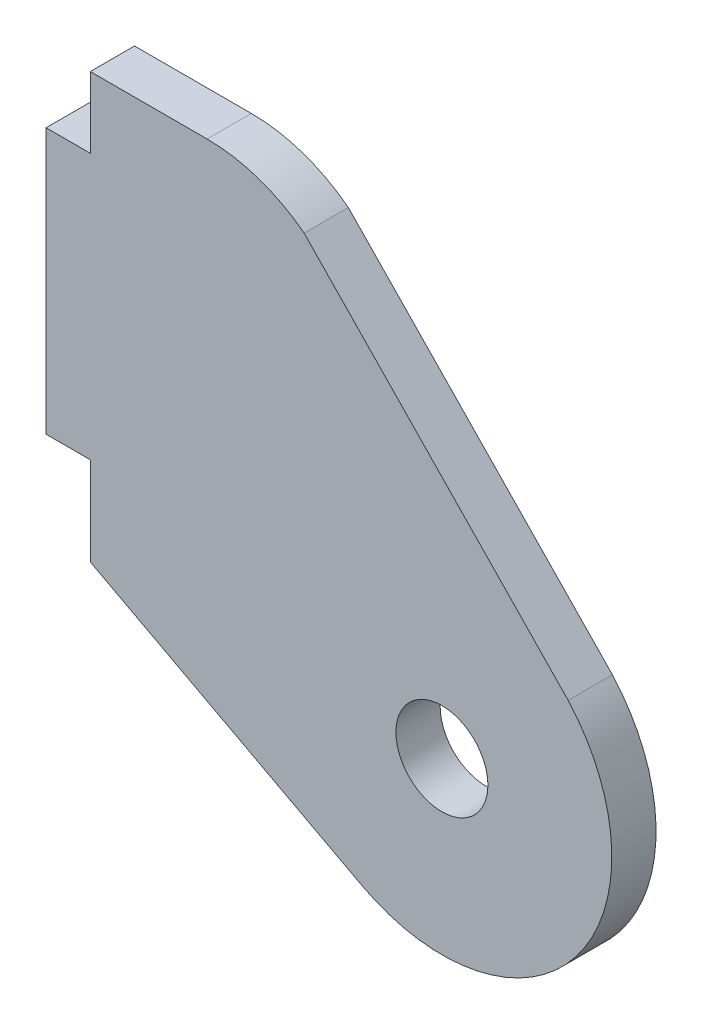
SolidWorks part; units mm, degrees
material "AISI 4130 Steel, annealed at 865C"
ref_plane "X-Y Datum" through (0, 0, 0) normal (0, 0, 1) x (1, 0, 0)
ref_plane "X-Z Datum" through (0, 0, 0) normal (0, 1, 0) x (1, 0, 0)
ref_plane "Y-Z Datum" through (0, 0, 0) normal (1, 0, 0) x (0, 0, -1)
sketch "Sketch1" plane through (0, 0, 0) normal (0, 0, 1) x (1, 0, 0)
  line L8 (-79.4095, -48.8706) -> (-79.4095, -29.8206)
  line L9 (-79.4095, -29.8206) -> (-76.2345, -29.8206)
  line L10 (-76.2345, -29.8206) -> (-76.2345, -24.7406)
  line L11 (-76.2345, -24.7406) -> (-67.8525, -24.7406)
  line L12 (-79.4095, -48.8706) -> (-76.2345, -48.8706)
  line L13 (-76.2345, -48.8706) -> (-76.2345, -55.2206)
  line L14 (-76.2345, -55.2206) -> (-56.7232, -65.595)
  line L18 (-60.8897, -27.1062) -> (-41.9389, -46.672)
  arc A2 (-56.7232, -65.595) -> (-41.9389, -46.672) centre (-50.9994, -54.8301) ccw
  arc A5 (-67.8525, -24.7406) -> (-60.8897, -27.1062) centre (-67.8525, -36.1706) cw
  dimension "D6" = 160
  dimension "D7" = 12.192
  dimension "D9" = 11.43
  dimension "D1" = 19.05
  dimension "D2" = 5.08
  dimension "D3" = 6.35
  dimension "D4" = 118
  dimension "D5" = 22.098
  dimension "D8" = 8.382
  dimension "D10" = 37.53
  dimension "D11" = 3.175
  dimension "D12" = 3.175
extrude "Boss-Extrude1" add sketch "Sketch1" along normal blind 3.175
hole_wizard "M6 Clearance Hole1" positions "Sketch2" profile "Sketch3" hole size "M6" standard "ANSI Metric"
sketch "Sketch2" plane through (0, 0, 0) normal (0, 0, -1) x (-1, 0, 0)
  point P0 (50.9994, -54.8301)
sketch "Sketch3" plane through (-50.9994, -54.8301, 0) normal (1, 0, 0) x (0, 1, 0)
  line L0 (0, 0) -> (0, 5.2848)
  line L1 (0, 5.2848) -> (3.3, 3.302)
  line L2 (3.3, 3.302) -> (3.3, 0)
  line L5 (3.3, 0) -> (0, 0)
  line L10 (0, 5.2848) -> (-3.3, 3.302) construction
  line L11 (0, -6.35) -> (0, 107.95) construction
  dimension "Hole Dia." = 6.6
  dimension "Hole Depth" = 3.302
  dimension "Drill Angle" = 118
